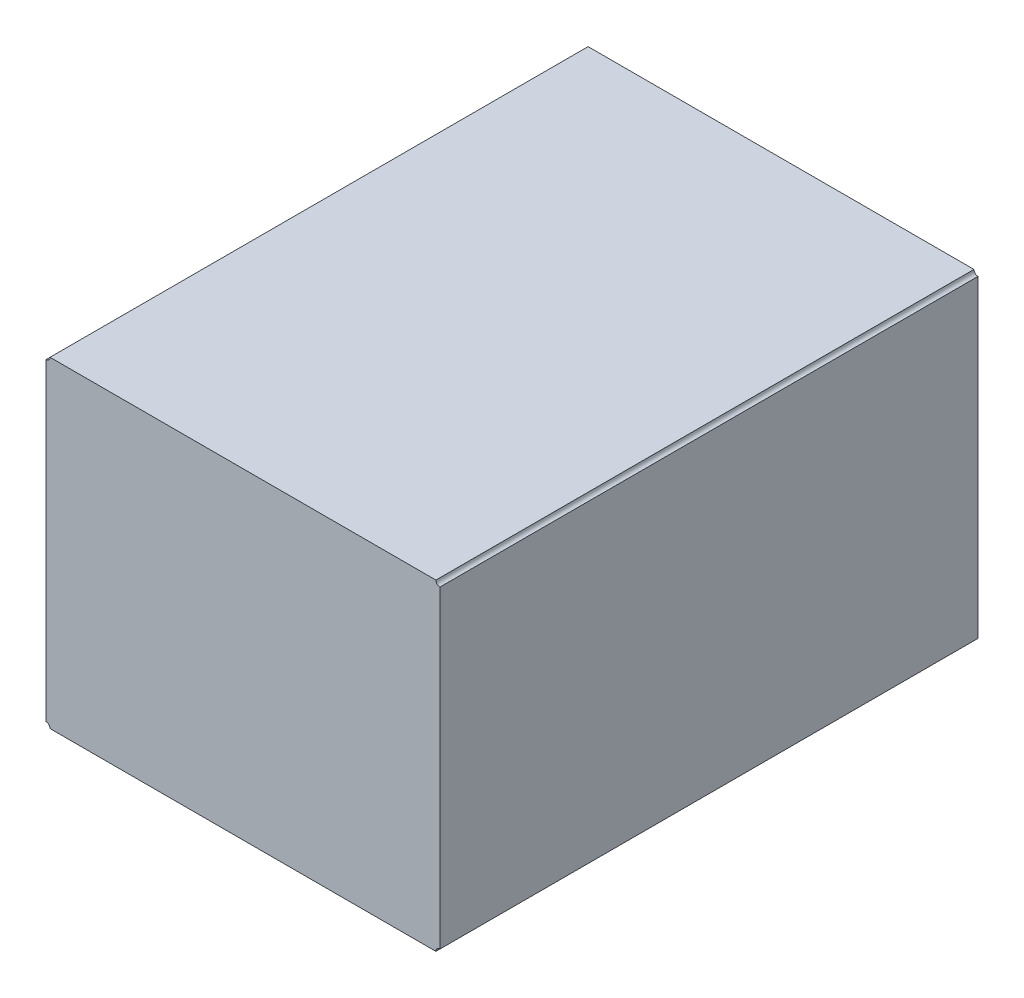
SolidWorks part; units mm, degrees
ref_plane "前视基准面" through (0, 0, 0) normal (0, 0, 1) x (1, 0, 0)
ref_plane "上视基准面" through (0, 0, 0) normal (0, 1, 0) x (1, 0, 0)
ref_plane "右视基准面" through (0, 0, 0) normal (1, 0, 0) x (0, 0, -1)
sketch "草图1" plane through (0, 0, 0) normal (0, 0, 1) x (1, 0, 0)
  line L0 (97.409, 85.344) -> (97.409, 90.424)
  line L1 (91.186, 85.344) -> (97.409, 85.344)
  line L2 (91.186, 85.344) -> (91.186, 90.424)
  line L3 (91.186, 90.424) -> (97.409, 90.424)
  circle A0 centre (97.409, 85.344) radius 0.0635
  circle A1 centre (97.409, 90.424) radius 0.0635
  circle A2 centre (91.186, 85.344) radius 0.0635
  circle A3 centre (97.409, 85.344) radius 0.0635
  circle A4 centre (91.186, 85.344) radius 0.0635
  circle A5 centre (91.186, 90.424) radius 0.0635
  circle A6 centre (91.186, 90.424) radius 0.0635
  circle A7 centre (97.409, 90.424) radius 0.0635
extrude "凸台-拉伸1" add sketch "草图1" along normal blind 8.5 contours A5 L2 A2 L1 A0 L0 A1 L3
